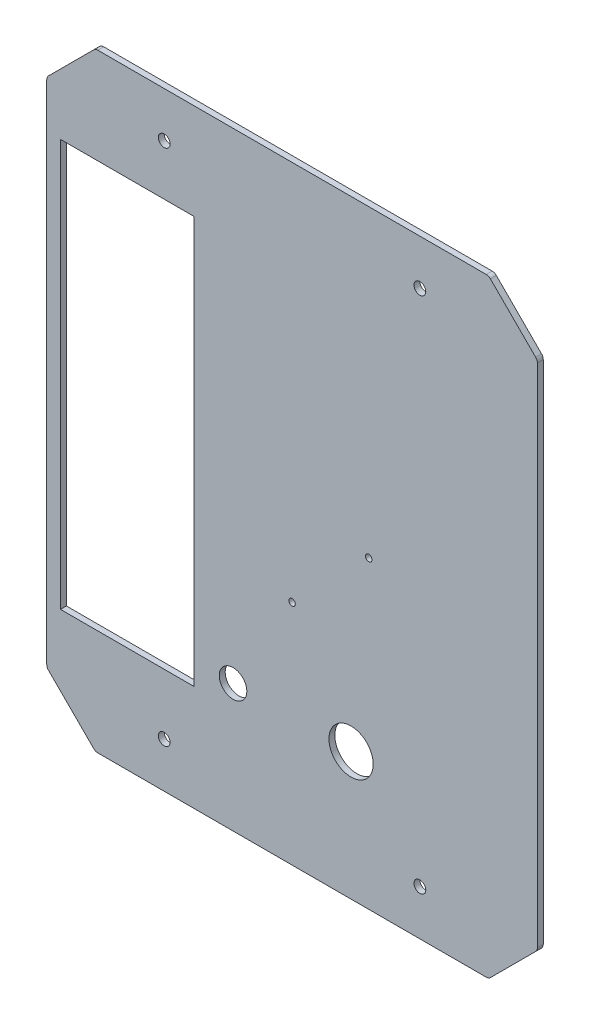
SolidWorks part; units mm, degrees
material "Verre"
ref_plane "Plan de dessus" through (0, 0, 0) normal (0, 0, 1) x (1, 0, 0)
ref_plane "Plan de droite" through (0, 0, 0) normal (0, 1, 0) x (1, 0, 0)
ref_plane "Plan de face" through (0, 0, 0) normal (1, 0, 0) x (0, 0, -1)
sketch "Esquisse1" plane through (0, 0, 0) normal (0, 0, 1) x (1, 0, 0)
  line L0 (0, 0) -> (-200, 0)
  line L1 (-200, 0) -> (-224.7487, 24.7487)
  line L2 (-224.7487, 24.7487) -> (-224.7487, 284.7487)
  line L3 (-224.7487, 284.7487) -> (-200, 309.4975)
  line L4 (-200, 309.4975) -> (0, 309.4975)
  line L5 (0, 309.4975) -> (24.7487, 284.7487)
  line L6 (24.7487, 284.7487) -> (24.7487, 24.7487)
  line L7 (24.7487, 24.7487) -> (0, 0)
  dimension "D1" = 260
  dimension "D2" = 35
  dimension "D3" = 135
  dimension "D4" = 200
extrude "Base" add sketch "Esquisse1" along normal blind 3
fillet "Congé1" radius 3 8 edges at (-200, 0, 1.5) (-224.7487, 24.7487, 1.5) (-224.7487, 284.7487, 1.5) (-200, 309.4975, 1.5) (0, 309.4975, 1.5) (24.7487, 284.7487, 1.5) (24.7487, 24.7487, 1.5) (0, 0, 1.5)
sketch "Esquisse19" plane through (0, 0, 0) normal (0, 0, -1) x (-1, 0, 0)
  line L0 (100, 309.4975) -> (100, 0) construction
  line L1 (1.2426, 309.4975) -> (198.7574, 309.4975) construction
  line L2 (198.7574, 0) -> (1.2426, 0) construction
  line L3 (-24.7487, 154.7487) -> (224.7487, 154.7487) construction
  line L4 (-24.7487, 25.9914) -> (-24.7487, 283.5061) construction
  line L5 (224.7487, 283.5061) -> (224.7487, 25.9914) construction
sketch "Esquisse20" plane through (0, 0, 0) normal (0, 0, -1) x (-1, 0, 0)
  line L0 (35, 286.4975) -> (35, 309.4975) construction
  line L1 (1.2426, 309.4975) -> (198.7574, 309.4975) construction
  line L2 (35, 286.4975) -> (100, 286.4975) construction
  line L3 (100, 309.4975) -> (100, 0) construction
  line L4 (100, 309.4975) -> (100, 0) construction
  line L5 (198.7574, 0) -> (1.2426, 0) construction
  line L6 (-24.7487, 154.7487) -> (224.7487, 154.7487) construction
  line L7 (-24.7487, 25.9914) -> (-24.7487, 283.5061) construction
  circle A0 centre (35, 286.4975) radius 3
  circle A1 centre (165, 286.4975) radius 3
  circle A2 centre (165, 23) radius 3
  circle A3 centre (35, 23) radius 3
  dimension "D3" = 6
  dimension "D1" = 65
  dimension "D2" = 23
extrude "Perçage Profilés" cut sketch "Esquisse20" against normal through all
sketch "Esquisse21" plane through (0, 0, 0) normal (0, 0, -1) x (-1, 0, 0)
  line L1 (100, 154.7487) -> (100, 115.7487) construction
  line L2 (100, 309.4975) -> (100, 0) construction
  line L3 (100, 154.7487) -> (61, 154.7487) construction
  line L4 (-24.7487, 154.7487) -> (224.7487, 154.7487) construction
  circle A1 centre (61, 154.7487) radius 1.65
  circle A2 centre (100, 115.7487) radius 1.65
  dimension "D2" = 3.3
  dimension "D1" = 39
extrude "Perçage Lidar" cut sketch "Esquisse21" against normal through all
sketch "Esquisse22" plane through (0, 0, 0) normal (0, 0, -1) x (-1, 0, 0)
  line L0 (100, 309.4975) -> (100, 0) construction
  line L1 (198.7574, 0) -> (1.2426, 0) construction
  circle A0 centre (70, 65) radius 11.25
  dimension "D1" = 22.5
  dimension "D2" = 30
  dimension "D3" = 65
extrude "Perçage Arret d'urgence" cut sketch "Esquisse22" against normal through all
sketch "Esquisse23" plane through (0, 0, 0) normal (0, 0, -1) x (-1, 0, 0)
  line L0 (198.7574, 0) -> (1.2426, 0) construction
  line L1 (100, 309.4975) -> (100, 0) construction
  circle A0 centre (130, 65) radius 7
  dimension "D1" = 14
  dimension "D2" = 65
  dimension "D3" = 30
extrude "Perçage Tirette" cut sketch "Esquisse23" against normal through all
sketch "Esquisse24" plane through (0, 0, 0) normal (0, 0, -1) x (-1, 0, 0)
  line L5 (149.7444, 260.7416) -> (217.7444, 260.7416)
  line L6 (149.7444, 260.7416) -> (149.7444, 53.7416)
  line L7 (149.7444, 53.7416) -> (217.7444, 53.7416)
  line L8 (217.7444, 260.7416) -> (217.7444, 53.7416)
  dimension "D1" = 68
  dimension "D2" = 207
extrude "Perçage Cable management" cut sketch "Esquisse24" against normal through all
